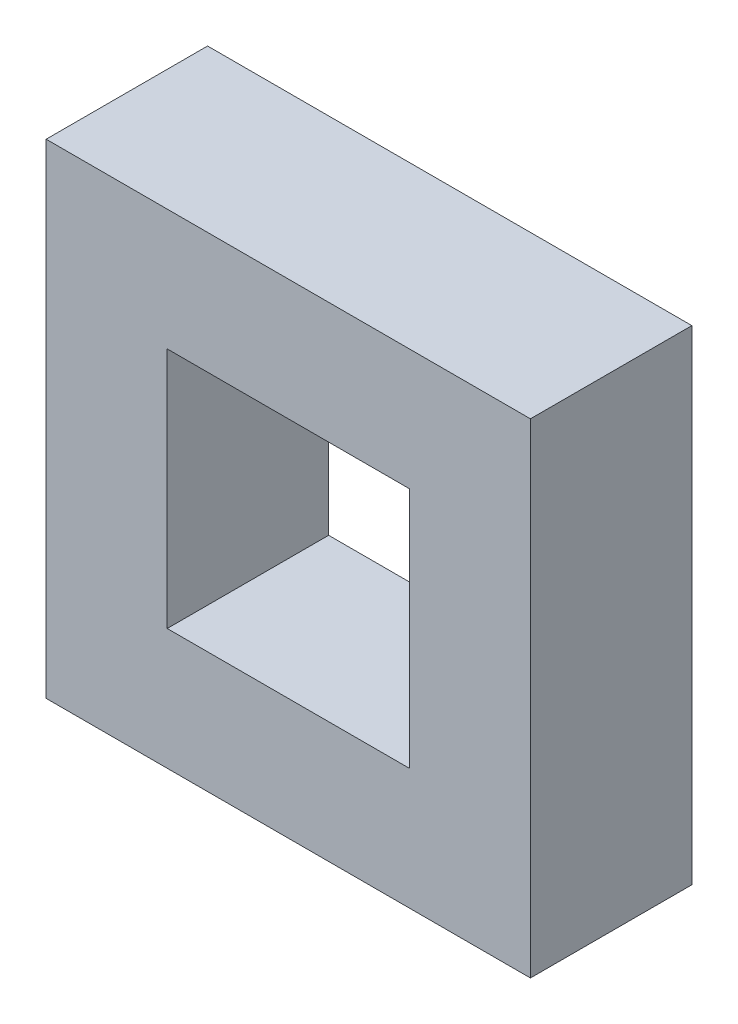
SolidWorks part; units mm, degrees
material "Copper"
ref_plane "Front Plane" through (0, 0, 0) normal (0, 0, 1) x (1, 0, 0)
ref_plane "Top Plane" through (0, 0, 0) normal (0, 1, 0) x (1, 0, 0)
ref_plane "Right Plane" through (0, 0, 0) normal (1, 0, 0) x (0, 0, -1)
sketch "Sketch1" plane through (0, 0, 0) normal (0, 0, 1) x (1, 0, 0)
  line L1 (-38.1, 38.1) -> (38.1, 38.1)
  line L2 (-38.1, 38.1) -> (-38.1, -38.1)
  line L3 (-38.1, -38.1) -> (38.1, -38.1)
  line L4 (38.1, 38.1) -> (38.1, -38.1)
  point P7 (1.4088, 2.0252)
  point P8 (90.5167, -20.1637)
  dimension "D1" = 38.1
  dimension "D2" = 38.1
  dimension "D3" = 38.1
  dimension "D4" = 38.1
extrude "Boss-Extrude1" add sketch "Sketch1" along normal mid plane 25.4
sketch "Sketch2" plane through (0, 0, 12.7) normal (0, 0, 1) x (1, 0, 0)
  line L1 (-19.05, 19.05) -> (19.05, 19.05)
  line L2 (-19.05, 19.05) -> (-19.05, -19.05)
  line L3 (-19.05, -19.05) -> (19.05, -19.05)
  line L4 (19.05, 19.05) -> (19.05, -19.05)
  dimension "D1" = 19.05
  dimension "D2" = 19.05
  dimension "D3" = 19.05
  dimension "D4" = 19.05
extrude "Cut-Extrude1" cut sketch "Sketch2" against normal through all
